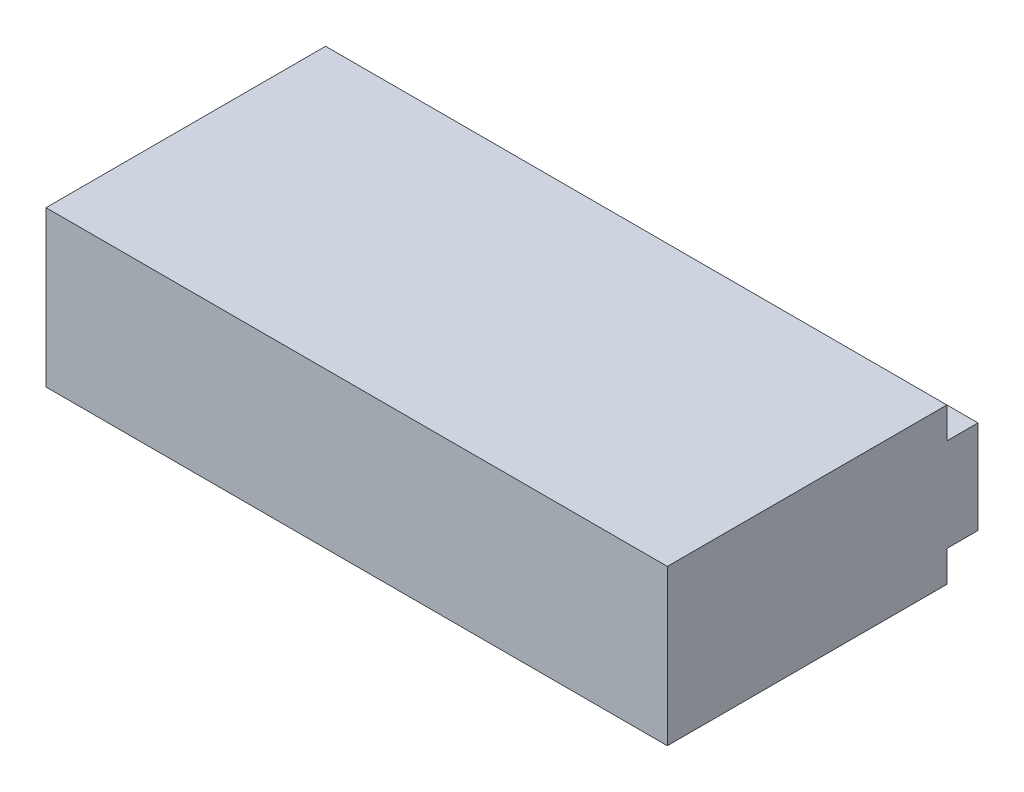
SolidWorks part; units mm, degrees
ref_plane "Přední rovina" through (0, 0, 0) normal (0, 0, 1) x (1, 0, 0)
ref_plane "Horní rovina" through (0, 0, 0) normal (0, 1, 0) x (1, 0, 0)
ref_plane "Pravá rovina" through (0, 0, 0) normal (1, 0, 0) x (0, 0, -1)
sketch "Skica1" plane through (0, 0, 0) normal (0, 0, 1) x (1, 0, 0)
  line L1 (5, 1.25) -> (-5, 1.25)
  line L2 (5, 1.25) -> (5, -1.25)
  line L3 (5, -1.25) -> (-5, -1.25)
  line L4 (-5, 1.25) -> (-5, -1.25)
  line L5 (5, 1.25) -> (-5, -1.25) construction
  line L6 (5, -1.25) -> (-5, 1.25) construction
  point P0 (0, 0)
  dimension "D1" = 10
  dimension "D2" = 2.5
extrude "Přidat vysunutím1" add sketch "Skica1" along normal blind 5
sketch "Skica2" plane through (5, 0, 0) normal (1, 0, 0) x (0, 0, -1)
  line L1 (0, 1.25) -> (-0.5, 1.25)
  line L2 (0, 1.25) -> (0, 0.75)
  line L3 (0, 0.75) -> (-0.5, 0.75)
  line L4 (-0.5, 1.25) -> (-0.5, 0.75)
  line L5 (0, -1.25) -> (-0.5, -1.25)
  line L6 (0, -1.25) -> (0, -0.75)
  line L7 (0, -0.75) -> (-0.5, -0.75)
  line L8 (-0.5, -1.25) -> (-0.5, -0.75)
  dimension "D1" = 0.5
  dimension "D2" = 0.5
  dimension "D3" = 0.5
  dimension "D4" = 0.5
extrude "Odebrat vysunutím1" cut sketch "Skica2" against normal through all
sketch "Skica3" plane through (0, 0, 0) normal (0, 0, -1) x (-1, 0, 0)
  line L0 (5, -0.75) -> (-5, -0.75) construction
  line L2 (5, 0.75) -> (-5, 0.75) construction
  circle A0 centre (0, 0) radius 0.25
  circle A1 centre (-2.54, 0) radius 0.25
  circle A2 centre (2.54, 0) radius 0.25
  point P7 (0, 0)
  point P8 (0, 0)
  dimension "D1" = 0.5
  dimension "D2" = 0.5
  dimension "D3" = 0.5
  dimension "D4" = 2.54
  dimension "D5" = 2.54
  dimension "D6" = 0.75
  dimension "D7" = 0.75
extrude "Odebrat vysunutím2" cut sketch "Skica3" against normal blind 1
